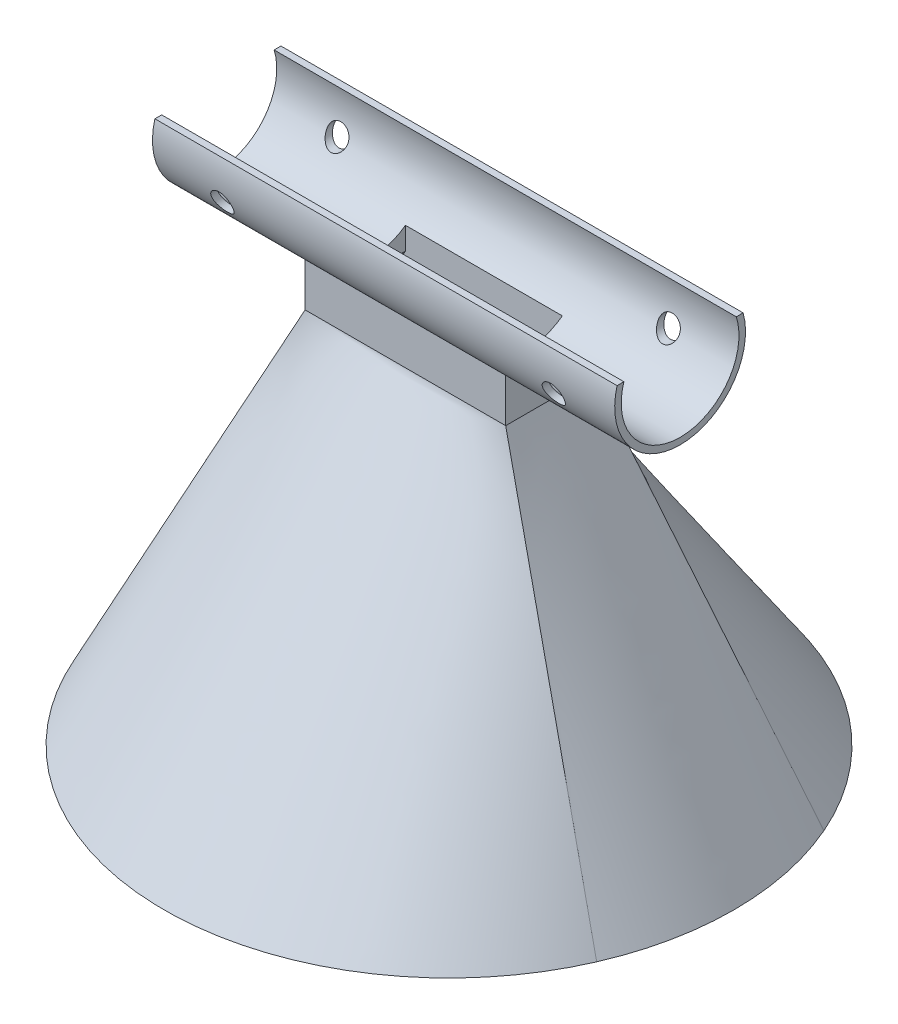
SolidWorks part; units mm, degrees
ref_plane "Front Plane" through (0, 0, 0) normal (0, 0, 1) x (1, 0, 0)
ref_plane "Top Plane" through (0, 0, 0) normal (0, 1, 0) x (1, 0, 0)
ref_plane "Right Plane" through (0, 0, 0) normal (1, 0, 0) x (0, 0, -1)
sketch "Sketch1" plane through (0, 0, 0) normal (0, 1, 0) x (1, 0, 0)
  circle A0 centre (0, 0) radius 65.3476
  dimension "D1" = 130.6952
ref_plane "Plane1" through (0, 80, 0) normal (0, 1, 0) x (1, 0, 0)
sketch "Sketch2" plane through (0, 80, 0) normal (0, 1, 0) x (1, 0, 0)
  line L1 (-23, 10) -> (23, 10)
  line L2 (-23, 10) -> (-23, -10)
  line L3 (-23, -10) -> (23, -10)
  line L4 (23, 10) -> (23, -10)
  line L5 (-23, 10) -> (23, -10) construction
  line L6 (-23, -10) -> (23, 10) construction
  point P0 (0, 0)
  dimension "D1" = 20
  dimension "D2" = 46
loft "Loft1" add profiles "Sketch2", "Sketch1"
sketch "Sketch3" plane through (0, 0, 0) normal (0, -1, 0) x (1, 0, 0)
  circle A0 centre (0, 0) radius 64
  dimension "D1" = 128
sketch "Sketch5" plane through (0, 80, 0) normal (0, 1, 0) x (1, 0, 0)
  line L0 (23, 10) -> (-23, 10) construction
  line L1 (-21, 8) -> (21, 8)
  line L2 (-21, 8) -> (-21, -8)
  line L3 (-21, -8) -> (21, -8)
  line L4 (21, 8) -> (21, -8)
  line L5 (-21, 8) -> (21, -8) construction
  line L6 (-21, -8) -> (21, 8) construction
  line L7 (23, -10) -> (23, 10) construction
  point P0 (0, 0)
  point P10 (23, 0)
  dimension "D1" = 2
  dimension "D2" = 2
loft "Cut-Loft3" cut profiles "Sketch5", "Sketch3"
sketch "Sketch12" plane through (0, 80, 0) normal (0, 1, 0) x (1, 0, 0)
  line L0 (-21, 8) -> (-21, -8) construction
  line L1 (21, 8) -> (-21, 8) construction
  line L2 (23, -10) -> (23, 10) construction
  line L3 (21, -8) -> (21, 8) construction
  line L4 (-21, -8) -> (21, -8) construction
  line L5 (-23, -10) -> (23, -10) construction
  line L6 (-23, 10) -> (-23, -10) construction
  line L7 (23, 10) -> (-23, 10) construction
  line L8 (-21, 8) -> (-21, -8)
  line L9 (21, 8) -> (-21, 8)
  line L10 (23, -10) -> (23, 10)
  line L11 (21, -8) -> (21, 8)
  line L12 (-21, -8) -> (21, -8)
  line L13 (-23, -10) -> (23, -10)
  line L14 (-23, 10) -> (-23, -10)
  line L15 (23, 10) -> (-23, 10)
extrude "Boss-Extrude5" add sketch "Sketch12" along normal blind 10
sketch "Sketch13" plane through (23, 0, 0) normal (1, 0, 0) x (0, 0, -1)
  line L0 (-12.8938, 105.1803) -> (-14.4568, 105.1803)
  line L1 (14.4568, 105.1803) -> (12.8938, 105.1803)
  arc A0 (-14.4568, 105.1803) -> (14.4568, 105.1803) centre (0, 101.1803) ccw
  arc A1 (-12.8938, 105.1803) -> (12.8938, 105.1803) centre (0, 101.1803) ccw
  dimension "D1" = 30
  dimension "D2" = 27
  dimension "D3" = 4
extrude "Boss-Extrude6" add sketch "Sketch13" against normal up to vertex (46 mm away) up to point (-23, 90, 10)
sketch "Sketch14" plane through (-23, 0, 0) normal (-1, 0, 0) x (0, 0, 1)
  line L0 (-12.8938, 105.1803) -> (12.8938, 105.1803)
  arc A0 (7.5664, 90) -> (12.8938, 105.1803) centre (0, 101.1803) ccw construction
  arc A1 (-12.8938, 105.1803) -> (12.8938, 105.1803) centre (0, 101.1803) ccw
  arc A2 (-12.8938, 105.1803) -> (-7.5664, 90) centre (0, 101.1803) ccw construction
extrude "Cut-Extrude5" cut sketch "Sketch14" against normal up to surface (46 mm away) up to face at (23, 94.769, 1)
sketch "Sketch15" plane through (0, 105.1803, 0) normal (0, 1, 0) x (1, 0, 0)
  line L1 (-18, 8) -> (18, 8)
  line L2 (-18, 8) -> (-18, -8)
  line L3 (-18, -8) -> (18, -8)
  line L4 (18, 8) -> (18, -8)
  line L5 (-18, 8) -> (18, -8) construction
  line L6 (-18, -8) -> (18, 8) construction
  point P0 (0, 0)
  dimension "D1" = 16
  dimension "D2" = 36
extrude "Cut-Extrude6" cut sketch "Sketch15" against normal blind 131
ref_plane "Plane4" through (0, 80, 0) normal (0, 1, 0) x (1, 0, 0)
sketch "Sketch20" plane through (0, 80, 0) normal (0, 1, 0) x (1, 0, 0)
  line L0 (-21, 8) -> (-18, 8) construction
  line L1 (-21, -8) -> (-21, 8) construction
  line L2 (-18, -8) -> (-18, 8) construction
  line L3 (-18, -8) -> (-21, -8) construction
  line L4 (-21, 8) -> (-18, 8)
  line L5 (-21, -8) -> (-21, 8)
  line L6 (-18, -8) -> (-18, 8)
  line L7 (-18, -8) -> (-21, -8)
  line L8 (21, -8) -> (18, -8) construction
  line L9 (21, 8) -> (21, -8) construction
  line L10 (18, 8) -> (21, 8) construction
  line L11 (18, 8) -> (18, -8) construction
  line L12 (21, -8) -> (18, -8)
  line L13 (21, 8) -> (21, -8)
  line L14 (18, 8) -> (21, 8)
  line L15 (18, 8) -> (18, -8)
extrude "Cut-Extrude7" cut sketch "Sketch20" along normal blind 26
sketch "Sketch21" plane through (21, 0, 0) normal (-1, 0, 0) x (0, 0, 1)
  line L0 (8, 90.3061) -> (8, 85.153)
  line L1 (8, 90.3061) -> (8, 80) construction
  line L2 (8, 85.153) -> (-8, 85.153)
  line L3 (-8, 90.3061) -> (-8, 80) construction
  line L4 (-8, 85.153) -> (-8, 90.3061)
  arc A0 (-8, 90.3061) -> (8, 90.3061) centre (0, 101.1803) ccw construction
  arc A1 (-8, 90.3061) -> (8, 90.3061) centre (0, 101.1803) ccw
extrude "Boss-Extrude8" add sketch "Sketch21" along normal blind 3
sketch "Sketch22" plane through (0, 0, -8) normal (0, 0, 1) x (1, 0, 0)
  line L0 (21, 85.153) -> (21, 80) construction
  line L1 (18, 85.153) -> (21, 85.153) construction
  line L2 (21, 85.153) -> (21, 80)
  line L3 (18, 85.153) -> (21, 85.153)
  line L4 (18, 85.153) -> (21, 80)
extrude "Boss-Extrude9" add sketch "Sketch22" along normal up to surface (16 mm away)
mirror "Mirror1" about plane through (0, 0, 0) normal (1, 0, 0) of "Boss-Extrude9", "Boss-Extrude8"
sketch "Sketch25" plane through (23, 0, 0) normal (1, 0, 0) x (0, 0, -1)
  line L0 (14.4568, 105.1803) -> (12.8938, 105.1803) construction
  line L1 (-12.8938, 105.1803) -> (-14.4568, 105.1803) construction
  line L2 (14.4568, 105.1803) -> (12.8938, 105.1803)
  line L3 (-12.8938, 105.1803) -> (-14.4568, 105.1803)
  arc A0 (10, 90) -> (14.4568, 105.1803) centre (0, 101.1803) ccw construction
  arc A1 (-14.4568, 105.1803) -> (-10, 90) centre (0, 101.1803) ccw construction
  arc A2 (-12.8938, 105.1803) -> (12.8938, 105.1803) centre (0, 101.1803) ccw construction
  arc A3 (10, 90) -> (14.4568, 105.1803) centre (0, 101.1803) ccw
  arc A4 (-14.4568, 105.1803) -> (-10, 90) centre (0, 101.1803) ccw
  arc A5 (-12.8938, 105.1803) -> (12.8938, 105.1803) centre (0, 101.1803) ccw
  arc A6 (-10, 90) -> (10, 90) centre (0, 101.1803) ccw
extrude "Boss-Extrude10" add sketch "Sketch25" along normal blind 30
sketch "Sketch26" plane through (-23, 0, 0) normal (-1, 0, 0) x (0, 0, 1)
  line L0 (12.8938, 105.1803) -> (14.4568, 105.1803) construction
  line L1 (-14.4568, 105.1803) -> (-12.8938, 105.1803) construction
  line L2 (12.8938, 105.1803) -> (14.4568, 105.1803)
  line L3 (-14.4568, 105.1803) -> (-12.8938, 105.1803)
  arc A0 (-14.4568, 105.1803) -> (-10, 90) centre (0, 101.1803) ccw construction
  arc A1 (10, 90) -> (14.4568, 105.1803) centre (0, 101.1803) ccw construction
  arc A2 (-12.8938, 105.1803) -> (12.8938, 105.1803) centre (0, 101.1803) ccw construction
  arc A3 (-14.4568, 105.1803) -> (-10, 90) centre (0, 101.1803) ccw
  arc A4 (10, 90) -> (14.4568, 105.1803) centre (0, 101.1803) ccw
  arc A5 (-12.8938, 105.1803) -> (12.8938, 105.1803) centre (0, 101.1803) ccw
  arc A6 (10, 90) -> (-10, 90) centre (0, 101.1803) cw
extrude "Boss-Extrude11" add sketch "Sketch26" along normal blind 30
sketch "Sketch27" plane through (0, 0, 10) normal (0, 0, 1) x (1, 0, 0)
  line L0 (0, 105.1803) -> (0, 80) construction
  line L1 (-53, 105.1803) -> (53, 105.1803) construction
  line L2 (-23, 80) -> (23, 80) construction
  line L3 (53, 95.6803) -> (-53, 96.4303) construction
  line L4 (53, 86.1803) -> (53, 105.1803) construction
  line L5 (-53, 105.1803) -> (-53, 87.6803) construction
  circle A0 centre (38, 95.7865) radius 2.5
  circle A1 centre (-38, 95.7865) radius 2.5
  dimension "D1" = 5
  dimension "D2" = 15
extrude "Cut-Extrude9" cut sketch "Sketch27" against normal through all and the other way through all
